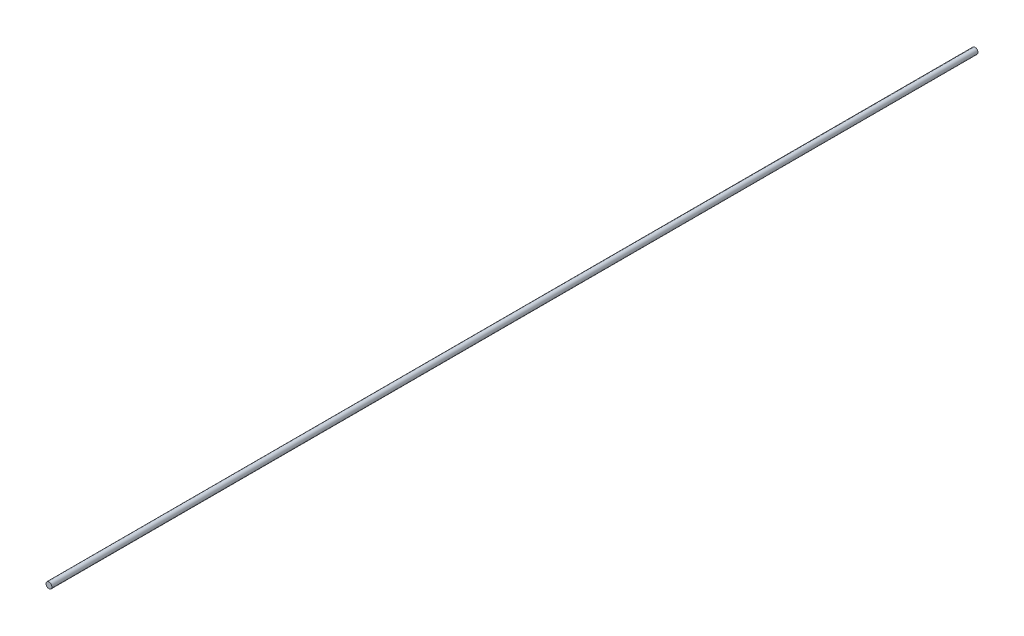
SolidWorks part; units mm, degrees
material "Hexcel AS4C (3000 Filaments)"
ref_plane "Front Plane" through (0, 0, 0) normal (0, 0, 1) x (1, 0, 0)
ref_plane "Top Plane" through (0, 0, 0) normal (0, 1, 0) x (1, 0, 0)
ref_plane "Right Plane" through (0, 0, 0) normal (1, 0, 0) x (0, 0, -1)
sketch "Sketch1" plane through (0, 0, 0) normal (0, 0, 1) x (1, 0, 0)
  circle A0 centre (0, 0) radius 8
  dimension "D1" = 16
extrude "Boss-Extrude1" add sketch "Sketch1" along normal blind 2500
